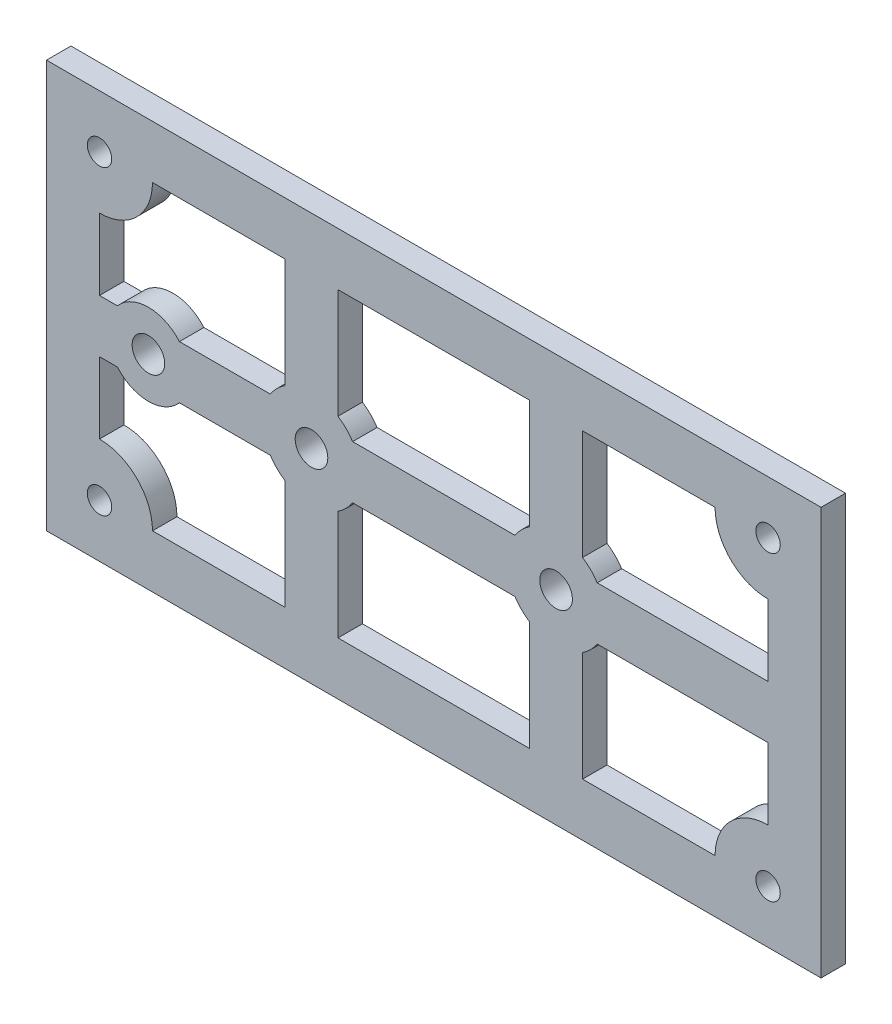
SolidWorks part; units mm, degrees
ref_plane "Front Plane" through (0, 0, 0) normal (0, 0, 1) x (1, 0, 0)
ref_plane "Top Plane" through (0, 0, 0) normal (0, 1, 0) x (1, 0, 0)
ref_plane "Right Plane" through (0, 0, 0) normal (1, 0, 0) x (0, 0, -1)
sketch "Sketch1" plane through (0, 0, 0) normal (0, 0, 1) x (1, 0, 0)
  line L1 (47.5, 25) -> (-47.5, 25)
  line L2 (47.5, 25) -> (47.5, -25)
  line L3 (47.5, -25) -> (-47.5, -25)
  line L4 (-47.5, 25) -> (-47.5, -25)
  line L5 (47.5, 25) -> (-47.5, -25) construction
  line L6 (47.5, -25) -> (-47.5, 25) construction
  point P0 (0, 0)
  dimension "D1" = 95
  dimension "D2" = 50
extrude "Boss-Extrude1" add sketch "Sketch1" along normal blind 3
sketch "Sketch2" plane through (0, 0, 3) normal (0, 0, 1) x (1, 0, 0)
  line L0 (-41, 18.5) -> (47.5, 18.5) construction
  line L1 (-47.5, 25) -> (-47.5, -25) construction
  line L2 (47.5, -25) -> (47.5, 25) construction
  line L3 (-47.5, 3.25) -> (-38.4686, 3.25) construction
  line L4 (47.5, 25) -> (-47.5, 25) construction
  line L5 (-41, 12) -> (-41, 3.25) construction
  line L6 (-41, 3.25) -> (-38.4686, 3.25) construction
  line L7 (-18.25, 25) -> (-18.25, 0) construction
  line L8 (-11.75, 25) -> (-11.75, 0) construction
  line L10 (-47.5, 0) -> (-38.75, 0) construction
  line L11 (-18.25, 18.6301) -> (-11.75, 18.6301) construction
  line L12 (-15, 18.6301) -> (-15, 6) construction
  line L14 (-11.75, 5.6292) -> (-11.75, 18.5)
  line L15 (-11.75, 18.5) -> (11.75, 18.5)
  line L16 (11.75, 18.6301) -> (18.25, 18.6301) construction
  line L17 (41, 25) -> (41, 3.25) construction
  line L18 (18.25, 25) -> (18.25, 0) construction
  line L19 (11.75, 25) -> (11.75, 0) construction
  line L20 (18.25, 18.5) -> (34.5, 18.5)
  line L21 (41, 12) -> (41, 3.25)
  line L22 (15, 18.6301) -> (15, 0) construction
  line L23 (11.75, -5.6292) -> (11.75, -11.5967) construction
  line L25 (11.75, 18.5) -> (11.75, 5.6292)
  line L26 (18.25, 5.6292) -> (18.25, 18.5)
  line L29 (-44.75, 0) -> (-32.75, 0) construction
  line L32 (-34.5, 18.5) -> (-18.25, 18.5)
  line L33 (-11.75, 5.6292) -> (-11.75, 5.0436)
  line L34 (-18.25, 18.5) -> (-18.25, 5.0436)
  line L35 (-15, 3.25) -> (-15, 0) construction
  line L37 (-41, 3.25) -> (-41, 12)
  line L39 (11.75, 5.6292) -> (11.75, 5.0436)
  line L40 (18.25, 5.6292) -> (18.25, 5.0436)
  line L43 (-41, 3.25) -> (-38.4686, 3.25)
  line L44 (41, 0) -> (47.5, 0) construction
  line L45 (41, 0) -> (41, -8.8807) construction
  line L46 (20.0436, 3.25) -> (47.5, 3.25) construction
  line L47 (20.0436, 3.25) -> (41, 3.25)
  line L48 (12.75, 0) -> (24.75, 0) construction
  line L49 (12.75, 0) -> (13.8809, 0)
  line L50 (-9.9564, 3.25) -> (9.9564, 3.25) construction
  line L51 (-9.9564, 3.25) -> (9.9564, 3.25)
  line L52 (-24.75, 0) -> (-12.75, 0) construction
  line L53 (-36.8274, 3.25) -> (-20.0436, 3.25) construction
  line L54 (-36.8274, 3.25) -> (-20.0436, 3.25)
  line L55 (-9.9564, 3.25) -> (9.9564, 3.25)
  arc A7 (41, 12) -> (34.5, 18.5) centre (41, 18.5) cw
  circle A8 centre (41, 18.5) radius 1.5
  arc A12 (-30, 0) -> (-29.8235, 2.294) centre (-15, 0) ccw construction
  arc A13 (-33.8483, 3.25) -> (-41.8152, 2.763) centre (-37.648, 0) ccw construction
  arc A14 (37.264, 3.25) -> (37.5, 0) centre (15, 0) ccw construction
  arc A15 (-41, 12) -> (-34.5, 18.5) centre (-41, 18.5) ccw
  circle A16 centre (-41, 18.5) radius 1.5
  arc A17 (-36.8274, 3.25) -> (-38.4686, 3.25) centre (-37.648, 0) ccw
  arc A18 (-18.25, 5.0436) -> (-20.0436, 3.25) centre (-15, 0) ccw
  arc A19 (11.75, 5.0436) -> (9.9564, 3.25) centre (15, 0) ccw
  arc A20 (-9.9564, 3.25) -> (-11.75, 5.0436) centre (-15, 0) ccw
  arc A21 (20.0436, 3.25) -> (18.25, 5.0436) centre (15, 0) ccw
  circle A22 centre (-35, 0) radius 5 construction
  dimension "D6" = 30
  dimension "D7" = 10
  dimension "D8" = 45
  dimension "D9" = 23.5
  dimension "D13" = 6.5
  dimension "D14" = 3
  dimension "D15" = 16.25
  dimension "D4" = 6.5
  dimension "D11" = 13
  dimension "D17" = 3
  dimension "D18" = 10
  dimension "D19" = 12
  dimension "D20" = 12
  dimension "D21" = 6
  dimension "D1" = 6.5
  dimension "D2" = 3.25
  dimension "D3" = 6.5
  dimension "D5" = 6.5
  dimension "15" = 29.25
  dimension "D10" = 6.5
  dimension "D12" = 6.5
  dimension "D16" = 16.25
sketch "Sketch3" plane through (0, 0, 3) normal (0, 0, 1) x (1, 0, 0)
  line L0 (-22, 5.0436) -> (-22, 18.5)
  line L1 (-22, 18.5) -> (-38.25, 18.5)
  line L2 (-44.75, 12) -> (-44.75, 3.25)
  line L3 (-44.75, 3.25) -> (-43.7936, 3.25)
  line L4 (-44.75, 0) -> (-32.75, 0) construction
  line L5 (-33.7064, 3.25) -> (-23.7936, 3.25)
  line L6 (-15.5, 18.5) -> (-15.5, 5.0436)
  line L9 (-9.9564, 3.25) -> (9.9564, 3.25) construction
  line L10 (-13.7064, 3.25) -> (13.7064, 3.25)
  line L11 (15.5, 18.5) -> (15.5, 5.0436)
  line L12 (15.5, 18.5) -> (-15.5, 18.5)
  line L13 (41, 25) -> (41, 3.25) construction
  line L14 (22, 5.0436) -> (22, 18.5)
  line L15 (22, 18.5) -> (38.25, 18.5)
  line L16 (23.7936, 3.25) -> (44.75, 3.25)
  line L17 (44.75, 3.25) -> (44.75, 12)
  arc A0 (-44.75, 12) -> (-38.25, 18.5) centre (-44.75, 18.5) ccw
  arc A1 (-43.7936, 3.25) -> (-33.7064, 3.25) centre (-38.75, 0) cw
  arc A2 (-36.8274, 3.25) -> (-38.4686, 3.25) centre (-37.648, 0) ccw construction
  circle A3 centre (-44.75, 18.5) radius 1.5
  arc A4 (-23.7936, 3.25) -> (-22, 5.0436) centre (-18.75, 0) cw
  arc A5 (-18.25, 5.0436) -> (-20.0436, 3.25) centre (-15, 0) ccw construction
  arc A6 (-15.5, 5.0436) -> (-13.7064, 3.25) centre (-18.75, 0) cw
  arc A7 (15.5, 5.0436) -> (13.7064, 3.25) centre (18.75, 0) ccw
  arc A8 (11.75, 5.0436) -> (9.9564, 3.25) centre (15, 0) ccw construction
  arc A9 (22, 5.0436) -> (23.7936, 3.25) centre (18.75, 0) cw
  arc A10 (20.0436, 3.25) -> (18.25, 5.0436) centre (15, 0) ccw construction
  arc A11 (38.25, 18.5) -> (44.75, 12) centre (44.75, 18.5) ccw
  circle A12 centre (44.75, 18.5) radius 1.5
sketch "Sketch4" plane through (0, 0, 3) normal (0, 0, 1) x (1, 0, 0)
  circle A0 centre (-15, 0) radius 2
  circle A2 centre (15, 0) radius 2
  circle A3 centre (-35, 0) radius 2
  dimension "D1" = 4
  dimension "D2" = 4
  dimension "D3" = 4
extrude "Cut-Extrude3" cut sketch "Sketch4" against normal through all
sketch "Sketch5" plane through (0, 0, 3) normal (0, 0, 1) x (1, 0, 0)
  line L0 (-34.5, 18.5) -> (-18.25, 18.5)
  line L1 (-18.25, 18.5) -> (-18.25, 5.0436)
  line L2 (-41, 12) -> (-41, 3.25)
  line L3 (-41, 3.25) -> (-38.7997, 3.25)
  line L4 (-11.75, 5.0436) -> (-11.75, 18.5)
  line L5 (-11.75, 18.5) -> (11.75, 18.5)
  line L6 (11.75, 18.5) -> (11.75, 5.0436)
  line L7 (9.9564, 3.25) -> (-9.9564, 3.25)
  line L8 (18.25, 5.0436) -> (18.25, 18.5)
  line L9 (18.25, 18.5) -> (34.5, 18.5)
  line L10 (41, 12) -> (41, 3.25)
  line L11 (41, 3.25) -> (20.0436, 3.25)
  line L12 (-31.2003, 3.25) -> (-20.0436, 3.25)
  arc A0 (-34.5, 18.5) -> (-41, 12) centre (-41, 18.5) cw
  arc A1 (-20.0436, 3.25) -> (-18.25, 5.0436) centre (-15, 0) cw
  arc A2 (-11.75, 5.0436) -> (-9.9564, 3.25) centre (-15, 0) cw
  arc A3 (11.75, 5.0436) -> (9.9564, 3.25) centre (15, 0) ccw
  arc A4 (18.25, 5.0436) -> (20.0436, 3.25) centre (15, 0) cw
  arc A5 (34.5, 18.5) -> (41, 12) centre (41, 18.5) ccw
  circle A6 centre (41, 18.5) radius 1.5
  circle A7 centre (-41, 18.5) radius 1.5
  arc A8 (-31.2003, 3.25) -> (-38.7997, 3.25) centre (-35, 0) ccw
extrude "Cut-Extrude4" cut sketch "Sketch5" against normal through all
mirror "Mirror2" about plane through (0, 0, 0) normal (0, 1, 0) of "Cut-Extrude4"
equation "\"w\"=95"
equation "\"h\"=50"
equation "\"D1@Sketch1\"= \"w\""
equation "\"D2@Sketch1\"= \"h\""
equation "\"hw\"= 4 * 6.5"
equation "\"big circle distance\"= 3.5mm"
